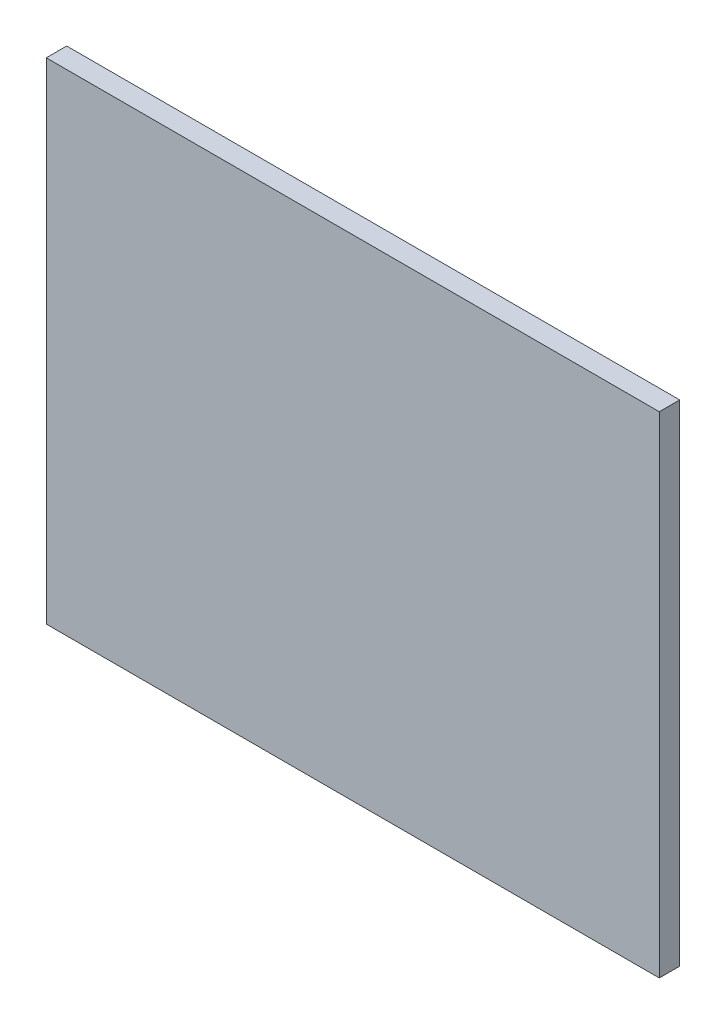
SolidWorks part; units mm, degrees
ref_plane "Front Plane" through (0, 0, 0) normal (0, 0, 1) x (1, 0, 0)
ref_plane "Top Plane" through (0, 0, 0) normal (0, 1, 0) x (1, 0, 0)
ref_plane "Right Plane" through (0, 0, 0) normal (1, 0, 0) x (0, 0, -1)
sketch "Sketch1" plane through (0, 0, 0) normal (0, 0, 1) x (1, 0, 0)
  line L1 (0, 0) -> (-381, 0)
  line L2 (0, 0) -> (0, 304.8)
  line L3 (0, 304.8) -> (-381, 304.8)
  line L4 (-381, 0) -> (-381, 304.8)
  dimension "D1" = 304.8
  dimension "D2" = 381
extrude "Boss-Extrude1" add sketch "Sketch1" along normal blind 12.7
